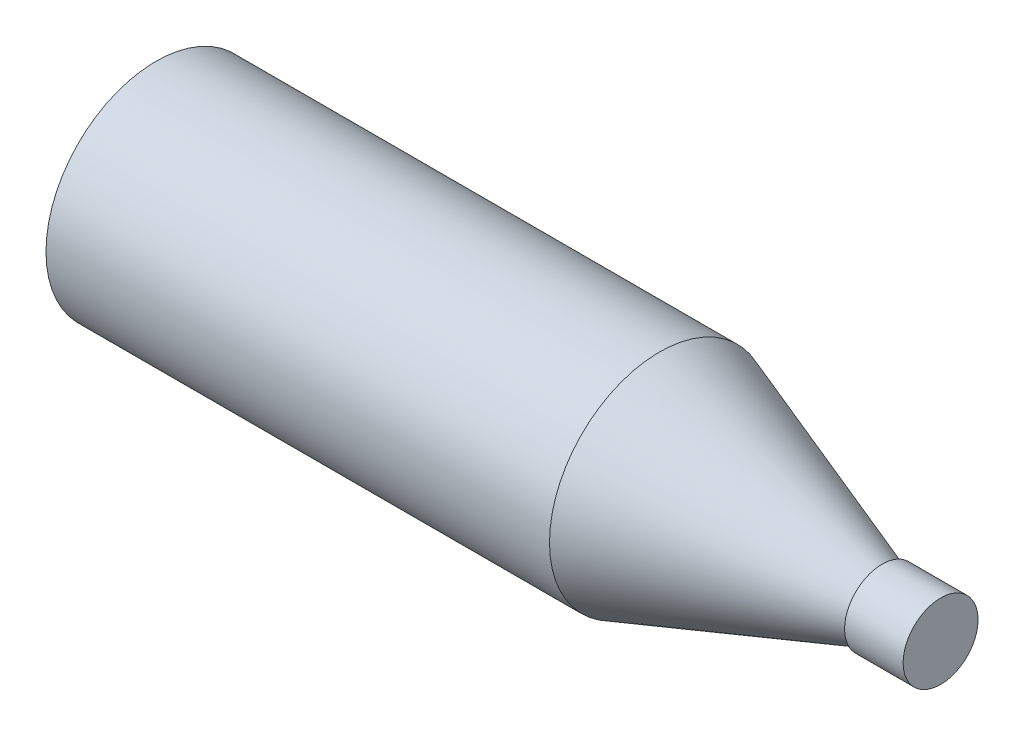
SolidWorks part; units mm, degrees
ref_plane "Спереди" through (0, 0, 0) normal (0, 0, 1) x (1, 0, 0)
ref_plane "Сверху" through (0, 0, 0) normal (0, 1, 0) x (1, 0, 0)
ref_plane "Справа" through (0, 0, 0) normal (1, 0, 0) x (0, 0, -1)
sketch "Эскиз1" plane through (0, 0, 0) normal (0, 0, 1) x (1, 0, 0)
  line L0 (-50.7749, 0) -> (101.9877, 0) construction
  line L1 (-50.7749, 0) -> (-50.7749, 47)
  line L2 (-50.7749, 47) -> (164.2251, 47)
  line L3 (164.2251, 47) -> (259.2251, 13.5)
  line L4 (259.2251, 13.5) -> (259.2251, 16)
  line L5 (259.2251, 16) -> (284.2251, 16)
  line L6 (284.2251, 16) -> (284.2251, 0)
  line L7 (-50.7749, 0) -> (284.2251, 0)
  point P8 (284.2251, 8)
  dimension "D1" = 94
  dimension "D2" = 27
  dimension "D3" = 32
  dimension "D4" = 25
  dimension "D5" = 335
  dimension "D6" = 120
revolve "Повернуть2" add sketch "Эскиз1" angle 360 about L0
